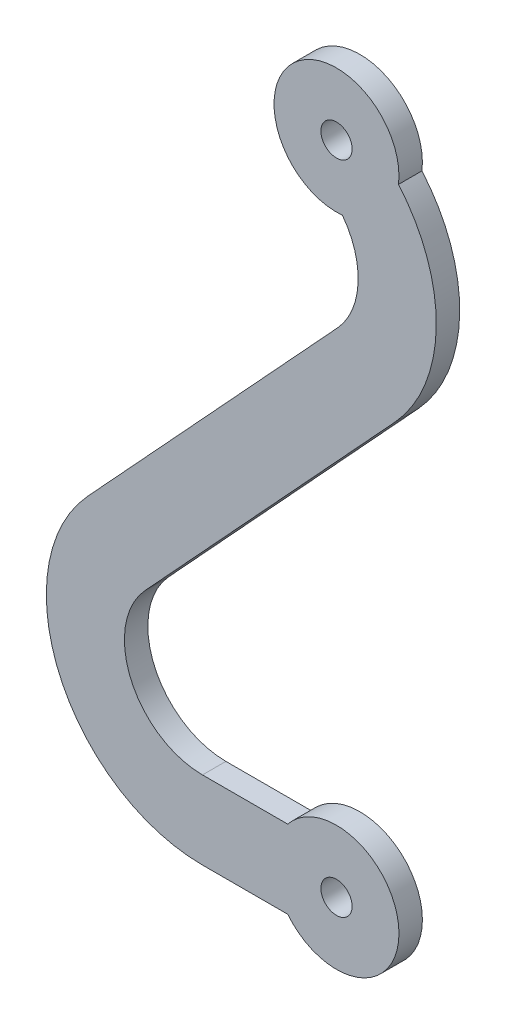
SolidWorks part; units mm, degrees
material "Galvanized Steel"
ref_plane "Front Plane" through (0, 0, 0) normal (0, 0, 1) x (1, 0, 0)
ref_plane "Top Plane" through (0, 0, 0) normal (0, 1, 0) x (1, 0, 0)
ref_plane "Right Plane" through (0, 0, 0) normal (1, 0, 0) x (0, 0, -1)
sketch "Sketch1" plane through (0, 0, 0) normal (0, 0, 1) x (1, 0, 0)
  line L0 (0, 0) -> (0, 42) construction
  line L1 (0, 2.5) -> (-8.582, 2.5) construction
  line L2 (-3.1225, 2.5) -> (-8.582, 2.5)
  line L3 (-3.1225, -2.5) -> (-8.582, -2.5)
  line L5 (-15.9309, 14.2819) -> (0.0634, 31.6135)
  line L6 (-12.2565, 10.8909) -> (3.7379, 28.2226)
  line L8 (0, -2.5) -> (-8.582, -2.5) construction
  line L9 (-1.7678, 40.2322) -> (-0.0755, 38.54) construction
  line L10 (1.7678, 43.7678) -> (3.46, 42.0755) construction
  circle A0 centre (0, 0) radius 1
  arc A1 (-3.1225, -2.5) -> (-3.1225, 2.5) centre (0, 0) ccw
  circle A2 centre (0, 42) radius 1
  arc A3 (3.9716, 41.5239) -> (0.3788, 38.018) centre (0, 42) ccw
  circle A4 centre (0, 0) radius 2.5 construction
  circle A5 centre (0, 42) radius 2.5 construction
  arc A6 (-8.582, 2.5) -> (-12.2565, 10.8909) centre (-8.582, 7.5) cw
  arc A7 (3.7379, 28.2226) -> (3.9716, 41.5239) centre (-3.611, 35.0044) ccw
  arc A8 (-8.582, -2.5) -> (-15.9309, 14.2819) centre (-8.582, 7.5) cw
  arc A9 (0.0634, 31.6135) -> (0.3788, 38.018) centre (-3.611, 35.0044) ccw
  arc A10 (3.7379, 28.2226) -> (3.46, 42.0755) centre (-3.611, 35.0044) ccw construction
  arc A11 (0.0634, 31.6135) -> (-0.0755, 38.54) centre (-3.611, 35.0044) ccw construction
  point P13 (12.2443, 32.4682)
  point P20 (-20, 2.5)
  point P23 (10.253, 35.2825)
  point P24 (0, 0)
  point P33 (5.3778, 36.9721)
  dimension "D1" = 2
  dimension "D2" = 8
  dimension "D4" = 8
  dimension "D5" = 2
  dimension "D6" = 5
  dimension "D7" = 5
  dimension "D10" = 5
  dimension "D11" = 10
  dimension "D15" = 5.4595
  dimension "D3" = 42
  dimension "D8" = 8.582
  dimension "D9" = 20
  dimension "D12" = 5
  dimension "D13" = 6.7175
  dimension "D14" = 10.253
  dimension "D16" = 3.9716
extrude "Boss-Extrude1" add sketch "Sketch1" along normal blind 1.5
